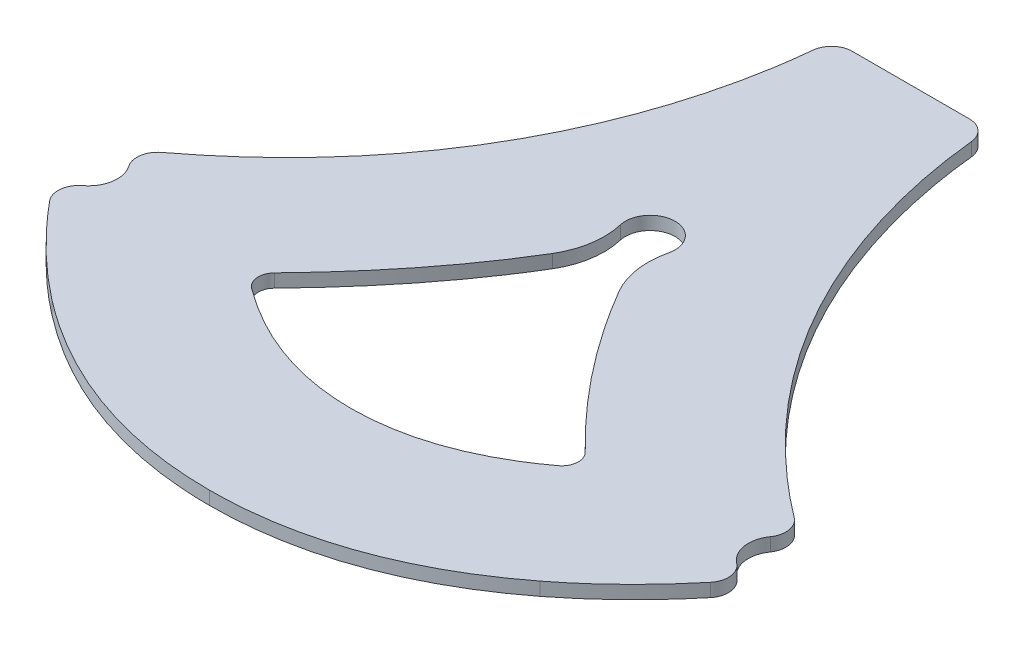
SolidWorks part; units mm, degrees
material "Default Heavy"
ref_plane "Front \"XY\"" through (0, 0, 0) normal (0, 0, 1) x (1, 0, 0)
ref_plane "Top \"XZ\"" through (0, 0, 0) normal (0, 1, 0) x (1, 0, 0)
ref_plane "Right \"YZ\"" through (0, 0, 0) normal (1, 0, 0) x (0, 0, -1)
sketch "Sketch1" plane through (0, -12.0818, 0) normal (0, 1, 0) x (1, 0, 0)
  line L4 (7.0683, 41.6006) -> (-7.0595, 41.6006)
  line L6 (7.0683, 41.6006) -> (-7.0595, 41.6006)
  arc A33 (-38.13, -10.5891) -> (-38.673, -14.0195) centre (-36.6252, -12.5855) ccw
  arc A34 (-39.4206, -18.8125) -> (-38.673, -14.0195) centre (-41.54, -16.0271) ccw
  arc A38 (-39.4206, -18.8125) -> (-39.832, -22.397) centre (-37.9068, -20.8021) ccw
  arc A39 (39.8378, -22.4011) -> (39.4269, -18.8166) centre (37.9129, -20.8059) ccw
  arc A40 (38.6795, -14.0241) -> (39.4269, -18.8166) centre (41.5466, -16.0315) ccw
  arc A41 (38.6795, -14.0241) -> (38.1364, -10.5939) centre (36.6316, -12.5902) ccw
  arc A42 (9.5562, 39.3464) -> (7.0683, 41.6006) centre (7.0683, 39.1006) ccw
  arc A43 (-7.0595, 41.6006) -> (-9.5474, 39.3464) centre (-7.0595, 39.1006) ccw
  arc A44 (-38.13, -10.5891) -> (-38.673, -14.0195) centre (-36.6252, -12.5855) ccw
  arc A45 (-39.4206, -18.8125) -> (-38.673, -14.0195) centre (-41.54, -16.0271) ccw
  arc A70 (-39.4206, -18.8125) -> (-39.832, -22.397) centre (-37.9068, -20.8021) ccw
  arc A71 (39.8378, -22.4011) -> (39.4269, -18.8166) centre (37.9129, -20.8059) ccw
  arc A72 (38.6795, -14.0241) -> (39.4269, -18.8166) centre (41.5466, -16.0315) ccw
  arc A73 (38.6795, -14.0241) -> (38.1364, -10.5939) centre (36.6316, -12.5902) ccw
  arc A74 (2.9171, 9.4772) -> (3.9511, 2.4687) centre (12.1546, 7.2595) ccw
  arc A75 (2.9171, 9.4772) -> (-2.9198, 9.4884) centre (0, 10.1775) ccw
  arc A81 (-4.0195, 2.4188) -> (-2.9198, 9.4884) centre (-12.1658, 7.3063) ccw
  arc A82 (-18.7595, -16.3733) -> (-18.4947, -19.3822) centre (-17.321, -17.7628) ccw
  arc A83 (18.4703, -19.4074) -> (18.7041, -16.3632) centre (17.2989, -17.7863) ccw
  arc A84 (2.9171, 9.4772) -> (3.9511, 2.4687) centre (12.1546, 7.2595) ccw
  arc A85 (2.9171, 9.4772) -> (-2.9198, 9.4884) centre (0, 10.1775) ccw
  arc A86 (-4.0195, 2.4188) -> (-2.9198, 9.4884) centre (-12.1658, 7.3063) ccw
  arc A87 (-18.7595, -16.3733) -> (-18.4947, -19.3822) centre (-17.321, -17.7628) ccw
  arc A88 (18.4703, -19.4074) -> (18.7041, -16.3632) centre (17.2989, -17.7863) ccw
  arc A89 (9.5562, 39.3464) -> (7.0683, 41.6006) centre (7.0683, 39.1006) ccw
  arc A90 (-7.0595, 41.6006) -> (-9.5474, 39.3464) centre (-7.0595, 39.1006) ccw
  spline S20 degree 3 poles (-361.1357, -9006.2412) (408.2007, 1023.6766) (-189.9273, 124.0647) (90.5106, -150.5904) (675.6401, 247.861) (5925.1762, 6688.6559) knots -44.189991 -44.189991 -44.189991 -44.189991 0.5 0.5 36.656885 36.656885 36.656885 36.656885 only from (-39.832, -22.397) to (-29.4307, -32.5394)
  spline S21 degree 3 poles (-5458.9807, -7160.509) (288.0292, 1163.494) (-198.9613, 61.9288) (-20.4604, -38.26) (-18.0451, -39.3754) (-14.2816, -40.7314) (-13.0141, -41.1265) (-10.4626, -41.8017) (-9.1771, -42.0821) (532.9278, -135.8371) (2755.8216, 9607.2036) (1449.1515, -1290.1086) knots -18.691493 -18.691493 -18.691493 -18.691493 0.25 0.25 0.5 0.5 0.625 0.625 0.75 0.75 52.944378 52.944378 52.944378 52.944378 only from (-29.4307, -32.5394) to (0.0044, -42.9764)
  spline S22 degree 3 poles (-83.0583, -8924.3195) (-816.3421, 2678.0036) (-279.5813, -92.3971) (9.2595, -42.0675) (10.5562, -41.7816) (13.107, -41.1014) (14.3628, -40.7068) (16.8364, -39.8119) (18.0542, -39.3118) (20.453, -38.2088) (21.6352, -37.6052) (199.0578, 61.9922) (-287.9926, 1164.7432) (5456.6153, -7163.0256) knots -27.11452 -27.11452 -27.11452 -27.11452 0.25 0.25 0.375 0.375 0.5 0.5 0.625 0.625 0.75 0.75 19.719987 19.719987 19.719987 19.719987 only from (0.0044, -42.9764) to (29.4355, -32.5422)
  spline S23 degree 3 poles (-2497.4272, 8560.7562) (-655.9836, 202.49) (-86.0813, -146.2484) (206.1007, 139.8782) (-568.1525, 1188.8875) (5991.7805, -6735.1983) knots -34.384152 -34.384152 -34.384152 -34.384152 0.5 0.5 49.852417 49.852417 49.852417 49.852417 only from (29.4355, -32.5422) to (39.8378, -22.4011)
  spline S24 degree 3 poles (-5230.3909, -7151.1905) (1948.6338, 1128.9285) (244.6684, -243.4554) (26.3668, 0.3497) (25.5637, 1.2946) (24.0142, 3.2162) (23.2668, 4.194) (21.1067, 7.1786) (19.7757, 9.2361) (17.3325, 13.4873) (16.2204, 15.6811) (14.7199, 19.076) (14.2467, 20.228) (13.3659, 22.5445) (12.9574, 23.7106) (11.8252, 27.2324) (11.1946, 29.6112) (-27.552, 214.2746) (637.6915, 571.7004) (8574.638, 2739.8271) knots -16.155295 -16.155295 -16.155295 -16.155295 0.25 0.25 0.3125 0.3125 0.375 0.375 0.5 0.5 0.625 0.625 0.6875 0.6875 0.75 0.75 0.875 0.875 10.328449 10.328449 10.328449 10.328449 only from (38.1364, -10.5939) to (9.5562, 39.3464)
  spline S25 degree 3 poles (-8658.0975, 2453.4979) (-703.6804, 575.1627) (29.2386, 221.9755) (-11.1913, 29.5904) (-11.826, 27.1987) (-13.3506, 22.4691) (-14.2312, 20.1617) (-16.2194, 15.6707) (-17.3273, 13.4849) (-19.7716, 9.2335) (-21.1079, 7.1677) (-23.287, 4.1607) (-24.0441, 3.1719) (-25.6008, 1.2452) (-26.402, 0.3048) (-261.0781, -261.3629) (-2273.2675, 1279.1753) (5393.2872, -6983.9462) knots -9.693628 -9.693628 -9.693628 -9.693628 0.125 0.125 0.25 0.25 0.375 0.375 0.5 0.5 0.625 0.625 0.6875 0.6875 0.75 0.75 18.503939 18.503939 18.503939 18.503939 only from (-9.5474, 39.3464) to (-38.13, -10.5891)
  spline S26 degree 3 poles (-39.832, -22.397) (-38.2832, -24.2664) (-36.6431, -26.0587) (-33.1743, -29.4559) (-31.352, -31.0548) (-29.4307, -32.5394) knots 0 0 0 0 0.5 0.5 1 1 1 1
  spline S27 degree 3 poles (-29.4307, -32.5394) (-27.3206, -34.1699) (-25.1109, -35.6497) (-20.4604, -38.26) (-18.0451, -39.3754) (-14.2816, -40.7314) (-13.0141, -41.1265) (-10.4626, -41.8017) (-9.1771, -42.0821) (-5.2915, -42.7541) (-2.6626, -42.9764) (0.0044, -42.9764) knots 0 0 0 0 0.25 0.25 0.5 0.5 0.625 0.625 0.75 0.75 1 1 1 1
  spline S28 degree 3 poles (0.0044, -42.9764) (2.6717, -42.9764) (5.3193, -42.7541) (9.2595, -42.0675) (10.5562, -41.7816) (13.107, -41.1014) (14.3628, -40.7068) (16.8364, -39.8119) (18.0542, -39.3118) (20.453, -38.2088) (21.6352, -37.6052) (25.1195, -35.6492) (27.3272, -34.1709) (29.4355, -32.5422) knots 0 0 0 0 0.25 0.25 0.375 0.375 0.5 0.5 0.625 0.625 0.75 0.75 1 1 1 1
  spline S29 degree 3 poles (29.4355, -32.5422) (31.3567, -31.058) (33.1832, -29.4556) (36.6518, -26.0589) (38.289, -24.2701) (39.8378, -22.4011) knots 0 0 0 0 0.5 0.5 1 1 1 1
  spline S30 degree 3 poles (38.1364, -10.5939) (34.1686, -7.603) (30.5094, -4.2768) (26.3668, 0.3497) (25.5637, 1.2946) (24.0142, 3.2162) (23.2668, 4.194) (21.1067, 7.1786) (19.7757, 9.2361) (17.3325, 13.4873) (16.2204, 15.6811) (14.7199, 19.076) (14.2467, 20.228) (13.3659, 22.5445) (12.9574, 23.7106) (11.8252, 27.2324) (11.1946, 29.6112) (10.1833, 34.4309) (9.8006, 36.8714) (9.5562, 39.3464) knots 0 0 0 0 0.25 0.25 0.3125 0.3125 0.375 0.375 0.5 0.5 0.625 0.625 0.6875 0.6875 0.75 0.75 0.875 0.875 1 1 1 1
  spline S31 degree 3 poles (-9.5474, 39.3464) (-9.7918, 36.8722) (-10.1748, 34.4273) (-11.1913, 29.5904) (-11.826, 27.1987) (-13.3506, 22.4691) (-14.2312, 20.1617) (-16.2194, 15.6707) (-17.3273, 13.4849) (-19.7716, 9.2335) (-21.1079, 7.1677) (-23.287, 4.1607) (-24.0441, 3.1719) (-25.6008, 1.2452) (-26.402, 0.3048) (-30.5182, -4.2848) (-34.1638, -7.5994) (-38.13, -10.5891) knots 0 0 0 0 0.125 0.125 0.25 0.25 0.375 0.375 0.5 0.5 0.625 0.625 0.6875 0.6875 0.75 0.75 1 1 1 1
  spline S33 degree 3 poles (-8423.8862, 3070.8277) (-196.453, 631.0114) (110.0496, 145.3413) (-12.0871, -8.969) (-13.3692, -10.4966) (-15.3493, -12.7369) (-16.0189, -13.4752) (-80.2953, -82.6348) (-244.7018, -61.9377) (6531.7724, -6177.7669) knots -23.901351 -23.901351 -23.901351 -23.901351 0.5 0.5 0.75 0.75 0.875 0.875 12.588314 12.588314 12.588314 12.588314 only from (-4.0195, 2.4188) to (-18.7595, -16.3733)
  spline S34 degree 3 poles (-4293.5555, -7936.5231) (-50.3766, 110.0419) (-54.4223, 5.6325) (-17.1355, -20.3479) (-16.7908, -20.5799) (-15.747, -21.2574) (-15.0382, -21.6843) (-12.8707, -22.886) (-11.3707, -23.5815) (-9.0251, -24.4414) (-8.2235, -24.6981) (-6.6138, -25.1376) (-5.804, -25.3212) (-3.3598, -25.7638) (-1.7106, -25.9143) (0.7936, -25.9184) (1.6348, -25.8822) (3.2938, -25.7361) (4.1158, -25.6264) (6.5599, -25.19) (8.16, -24.7562) (10.518, -23.8999) (11.2939, -23.5809) (12.8082, -22.888) (13.5495, -22.5131) (15.0027, -21.7105) (15.7146, -21.2829) (16.7621, -20.605) (17.1079, -20.3728) (54.5018, 5.6202) (48.809, 108.0735) (4514.6713, -7812.9902) knots -3.348669 -3.348669 -3.348669 -3.348669 0.03125 0.03125 0.0625 0.0625 0.125 0.125 0.25 0.25 0.3125 0.3125 0.375 0.375 0.5 0.5 0.5625 0.5625 0.625 0.625 0.75 0.75 0.8125 0.8125 0.875 0.875 0.9375 0.9375 0.96875 0.96875 4.349856 4.349856 4.349856 4.349856 only from (-18.4947, -19.3822) to (18.4703, -19.4074)
  spline S53 degree 3 poles (-6295.3391, -6420.8441) (241.7112, -32.3679) (75.1144, -75.141) (15.8981, -13.5111) (15.217, -12.7784) (13.2098, -10.546) (11.9226, -9.0147) (-199.8505, 260.9693) (1210.8718, 1641.0125) (7479.9657, 4881.6019) knots -10.431592 -10.431592 -10.431592 -10.431592 0.125 0.125 0.25 0.25 0.5 0.5 43.112125 43.112125 43.112125 43.112125 only from (18.7041, -16.3632) to (3.9511, 2.4687)
  spline S54 degree 3 poles (-4.0195, 2.4188) (-6.0734, -1.0046) (-8.3712, -4.2742) (-12.0871, -8.969) (-13.3692, -10.4966) (-15.3493, -12.7369) (-16.0189, -13.4752) (-17.3762, -14.9357) (-18.0664, -15.6558) (-18.7595, -16.3733) knots 0 0 0 0 0.5 0.5 0.75 0.75 0.875 0.875 1 1 1 1
  spline S55 degree 3 poles (-18.4947, -19.3822) (-18.1567, -19.6272) (-17.8187, -19.8719) (-17.1355, -20.3479) (-16.7908, -20.5799) (-15.747, -21.2574) (-15.0382, -21.6843) (-12.8707, -22.886) (-11.3707, -23.5815) (-9.0251, -24.4414) (-8.2235, -24.6981) (-6.6138, -25.1376) (-5.804, -25.3212) (-3.3598, -25.7638) (-1.7106, -25.9143) (0.7936, -25.9184) (1.6348, -25.8822) (3.2938, -25.7361) (4.1158, -25.6264) (6.5599, -25.19) (8.16, -24.7562) (10.518, -23.8999) (11.2939, -23.5809) (12.8082, -22.888) (13.5495, -22.5131) (15.0027, -21.7105) (15.7146, -21.2829) (16.7621, -20.605) (17.1079, -20.3728) (17.7928, -19.8967) (18.1316, -19.6522) (18.4703, -19.4074) knots 0 0 0 0 0.03125 0.03125 0.0625 0.0625 0.125 0.125 0.25 0.25 0.3125 0.3125 0.375 0.375 0.5 0.5 0.5625 0.5625 0.625 0.625 0.75 0.75 0.8125 0.8125 0.875 0.875 0.9375 0.9375 0.96875 0.96875 1 1 1 1
  spline S56 degree 3 poles (18.7041, -16.3632) (17.9921, -15.6602) (17.284, -14.9535) (15.8981, -13.5111) (15.217, -12.7784) (13.2098, -10.546) (11.9226, -9.0147) (8.217, -4.2905) (5.9698, -0.988) (3.9511, 2.4687) knots 0 0 0 0 0.125 0.125 0.25 0.25 0.5 0.5 1 1 1 1
  dimension "D1" = 0.5
  dimension "D2" = 0.5
extrude "Boss-Extrude1" add sketch "Sketch1" along normal blind 1.6
sketch "Sketch2" plane through (0, -10.4818, 0) normal (0, 1, 0) x (1, 0, 0)
  line L0 (0.0044, 41.6006) -> (0.0044, 33.6006)
  line L1 (7.0683, 41.6006) -> (-7.0595, 41.6006) construction
  line L2 (0.0044, -42.9764) -> (0.0044, -34.9764)
  line L3 (-25.2799, -35.4613) -> (-20.9815, -28.7141)
  line L4 (25.2885, -35.4609) -> (20.9901, -28.7138)
  line L5 (7.0683, 41.6006) -> (-7.0595, 41.6006)
  arc A0 (9.5562, 39.3464) -> (7.0683, 41.6006) centre (7.0683, 39.1006) ccw construction
  arc A1 (-7.0595, 41.6006) -> (-9.5474, 39.3464) centre (-7.0595, 39.1006) ccw construction
  arc A2 (-38.13, -10.5891) -> (-38.673, -14.0195) centre (-36.6252, -12.5855) ccw construction
  arc A3 (-39.4206, -18.8125) -> (-38.673, -14.0195) centre (-41.54, -16.0271) ccw construction
  arc A4 (-39.4206, -18.8125) -> (-39.832, -22.397) centre (-37.9068, -20.8021) ccw construction
  arc A5 (39.8378, -22.4011) -> (39.4269, -18.8166) centre (37.9129, -20.8059) ccw construction
  arc A6 (38.6795, -14.0241) -> (39.4269, -18.8166) centre (41.5466, -16.0315) ccw construction
  arc A7 (38.6795, -14.0241) -> (38.1364, -10.5939) centre (36.6316, -12.5902) ccw construction
  arc A8 (9.5562, 39.3464) -> (7.0683, 41.6006) centre (7.0683, 39.1006) ccw
  arc A9 (-7.0595, 41.6006) -> (-9.5474, 39.3464) centre (-7.0595, 39.1006) ccw
  arc A10 (-38.13, -10.5891) -> (-38.673, -14.0195) centre (-36.6252, -12.5855) ccw
  arc A11 (-39.4206, -18.8125) -> (-38.673, -14.0195) centre (-41.54, -16.0271) ccw
  arc A12 (-39.4206, -18.8125) -> (-39.832, -22.397) centre (-37.9068, -20.8021) ccw
  arc A13 (39.8378, -22.4011) -> (39.4269, -18.8166) centre (37.9129, -20.8059) ccw
  arc A14 (38.6795, -14.0241) -> (39.4269, -18.8166) centre (41.5466, -16.0315) ccw
  arc A15 (38.6795, -14.0241) -> (38.1364, -10.5939) centre (36.6316, -12.5902) ccw
  arc A16 (-18.7595, -16.3733) -> (-18.4947, -19.3822) centre (-17.321, -17.7628) ccw construction
  arc A17 (18.4703, -19.4074) -> (18.7041, -16.3632) centre (17.2989, -17.7863) ccw construction
  arc A18 (2.9171, 9.4772) -> (3.9511, 2.4687) centre (12.1546, 7.2595) ccw construction
  arc A19 (2.9171, 9.4772) -> (-2.9198, 9.4884) centre (0, 10.1775) ccw construction
  arc A20 (-4.0195, 2.4188) -> (-2.9198, 9.4884) centre (-12.1658, 7.3063) ccw construction
  arc A21 (-18.7595, -16.3733) -> (-18.4947, -19.3822) centre (-17.321, -17.7628) ccw
  arc A22 (18.4703, -19.4074) -> (18.7041, -16.3632) centre (17.2989, -17.7863) ccw
  arc A23 (2.9171, 9.4772) -> (3.9511, 2.4687) centre (12.1546, 7.2595) ccw
  arc A24 (2.9171, 9.4772) -> (-2.9198, 9.4884) centre (0, 10.1775) ccw
  arc A25 (-4.0195, 2.4188) -> (-2.9198, 9.4884) centre (-12.1658, 7.3063) ccw
  spline S0 degree 3 poles (-1424.0562, -1442.6952) (28.6907, 516.1598) (-137.4092, 27.3809) (-20.4604, -38.26) (-18.0451, -39.3754) (-14.2816, -40.7314) (-13.0141, -41.1265) (-10.4626, -41.8017) (-9.1771, -42.0821) (158.4711, -71.0762) (483.979, 830.8672) (816.9599, 1776.512) knots -12.073737 -12.073737 -12.073737 -12.073737 0.25 0.25 0.5 0.5 0.625 0.625 0.75 0.75 16.804983 16.804983 16.804983 16.804983 only from (-29.4307, -32.5394) to (0.0044, -42.9764) construction
  spline S1 degree 3 poles (-29.4307, -32.5394) (-27.3206, -34.1699) (-25.1109, -35.6497) (-20.4604, -38.26) (-18.0451, -39.3754) (-14.2816, -40.7314) (-13.0141, -41.1265) (-10.4626, -41.8017) (-9.1771, -42.0821) (-5.2915, -42.7541) (-2.6626, -42.9764) (0.0044, -42.9764) knots 0 0 0 0 0.25 0.25 0.5 0.5 0.625 0.625 0.75 0.75 1 1 1 1 construction
  spline S2 degree 3 poles (0.0044, -42.9764) (2.6717, -42.9764) (5.3193, -42.7541) (9.2595, -42.0675) (10.5562, -41.7816) (13.107, -41.1014) (14.3628, -40.7068) (16.8364, -39.8119) (18.0542, -39.3118) (20.453, -38.2088) (21.6352, -37.6052) (25.1195, -35.6492) (27.3272, -34.1709) (29.4355, -32.5422) knots 0 0 0 0 0.25 0.25 0.375 0.375 0.5 0.5 0.625 0.625 0.75 0.75 1 1 1 1 construction
  spline S3 degree 3 poles (-440.2453, -1934.8699) (-519.17, 1279.8396) (-194.086, -77.4998) (9.2595, -42.0675) (10.5562, -41.7816) (13.107, -41.1014) (14.3628, -40.7068) (16.8364, -39.8119) (18.0542, -39.3118) (20.453, -38.2088) (21.6352, -37.6052) (137.4809, 27.4256) (-28.6443, 516.76) (1423.6331, -1443.0733) knots -18.977772 -18.977772 -18.977772 -18.977772 0.25 0.25 0.375 0.375 0.5 0.5 0.625 0.625 0.75 0.75 13.09281 13.09281 13.09281 13.09281 only from (0.0044, -42.9764) to (29.4355, -32.5422) construction
  spline S4 degree 3 poles (-1867.0337, 761.7677) (-214.1809, 300.124) (11.968, 139.7937) (-11.1913, 29.5904) (-11.826, 27.1987) (-13.3506, 22.4691) (-14.2312, 20.1617) (-16.2194, 15.6707) (-17.3273, 13.4849) (-19.7716, 9.2335) (-21.1079, 7.1677) (-23.287, 4.1607) (-24.0441, 3.1719) (-25.6008, 1.2452) (-26.402, 0.3048) (-188.6003, -180.5489) (-1196.8152, 497.2845) (713.0433, -1780.6166) knots -5.445972 -5.445972 -5.445972 -5.445972 0.125 0.125 0.25 0.25 0.375 0.375 0.5 0.5 0.625 0.625 0.6875 0.6875 0.75 0.75 13.001475 13.001475 13.001475 13.001475 only from (-9.5474, 39.3464) to (-38.13, -10.5891) construction
  spline S5 degree 3 poles (34.5014, -2019.1221) (83.4289, 488.7085) (-136.0537, 71.302) (37.1209, -98.3016) (260.7778, 3.0906) (1432.5412, 1322.2518) knots -28.658886 -28.658886 -28.658886 -28.658886 0.5 0.5 21.265271 21.265271 21.265271 21.265271 only from (-39.832, -22.397) to (-29.4307, -32.5394) construction
  spline S6 degree 3 poles (-807.9187, 1769.9142) (-261.6301, -5.9472) (-36.08, -97.2833) (147.6142, 82.6039) (-149.4521, 574.9626) (1506.1611, -1362.4779) knots -19.968685 -19.968685 -19.968685 -19.968685 0.5 0.5 32.99067 32.99067 32.99067 32.99067 only from (29.4355, -32.5422) to (39.8378, -22.4011) construction
  spline S7 degree 3 poles (-725.1623, -1795.2036) (1009.533, 415.4628) (175.0079, -165.6568) (26.3668, 0.3497) (25.5637, 1.2946) (24.0142, 3.2162) (23.2668, 4.194) (21.1067, 7.1786) (19.7757, 9.2361) (17.3325, 13.4873) (16.2204, 15.6811) (14.7199, 19.076) (14.2467, 20.228) (13.3659, 22.5445) (12.9574, 23.7106) (11.8252, 27.2324) (11.1946, 29.6112) (-11.0987, 135.8594) (195.4726, 296.5607) (1845.1699, 816.6095) knots -10.900393 -10.900393 -10.900393 -10.900393 0.25 0.25 0.3125 0.3125 0.375 0.375 0.5 0.5 0.625 0.625 0.6875 0.6875 0.75 0.75 0.875 0.875 6.261071 6.261071 6.261071 6.261071 only from (38.1364, -10.5939) to (9.5562, 39.3464) construction
  spline S8 degree 3 poles (-9.5474, 39.3464) (-9.7918, 36.8722) (-10.1748, 34.4273) (-11.1913, 29.5904) (-11.826, 27.1987) (-13.3506, 22.4691) (-14.2312, 20.1617) (-16.2194, 15.6707) (-17.3273, 13.4849) (-19.7716, 9.2335) (-21.1079, 7.1677) (-23.287, 4.1607) (-24.0441, 3.1719) (-25.6008, 1.2452) (-26.402, 0.3048) (-30.5182, -4.2848) (-34.1638, -7.5994) (-38.13, -10.5891) knots 0 0 0 0 0.125 0.125 0.25 0.25 0.375 0.375 0.5 0.5 0.625 0.625 0.6875 0.6875 0.75 0.75 1 1 1 1
  spline S9 degree 3 poles (-39.832, -22.397) (-38.2832, -24.2664) (-36.6431, -26.0587) (-33.1743, -29.4559) (-31.352, -31.0548) (-29.4307, -32.5394) knots 0 0 0 0 0.5 0.5 1 1 1 1
  spline S10 degree 3 poles (-29.4307, -32.5394) (-27.3206, -34.1699) (-25.1109, -35.6497) (-20.4604, -38.26) (-18.0451, -39.3754) (-14.2816, -40.7314) (-13.0141, -41.1265) (-10.4626, -41.8017) (-9.1771, -42.0821) (-5.2915, -42.7541) (-2.6626, -42.9764) (0.0044, -42.9764) knots 0 0 0 0 0.25 0.25 0.5 0.5 0.625 0.625 0.75 0.75 1 1 1 1
  spline S11 degree 3 poles (0.0044, -42.9764) (2.6717, -42.9764) (5.3193, -42.7541) (9.2595, -42.0675) (10.5562, -41.7816) (13.107, -41.1014) (14.3628, -40.7068) (16.8364, -39.8119) (18.0542, -39.3118) (20.453, -38.2088) (21.6352, -37.6052) (25.1195, -35.6492) (27.3272, -34.1709) (29.4355, -32.5422) knots 0 0 0 0 0.25 0.25 0.375 0.375 0.5 0.5 0.625 0.625 0.75 0.75 1 1 1 1
  spline S12 degree 3 poles (29.4355, -32.5422) (31.3567, -31.058) (33.1832, -29.4556) (36.6518, -26.0589) (38.289, -24.2701) (39.8378, -22.4011) knots 0 0 0 0 0.5 0.5 1 1 1 1
  spline S13 degree 3 poles (38.1364, -10.5939) (34.1686, -7.603) (30.5094, -4.2768) (26.3668, 0.3497) (25.5637, 1.2946) (24.0142, 3.2162) (23.2668, 4.194) (21.1067, 7.1786) (19.7757, 9.2361) (17.3325, 13.4873) (16.2204, 15.6811) (14.7199, 19.076) (14.2467, 20.228) (13.3659, 22.5445) (12.9574, 23.7106) (11.8252, 27.2324) (11.1946, 29.6112) (10.1833, 34.4309) (9.8006, 36.8714) (9.5562, 39.3464) knots 0 0 0 0 0.25 0.25 0.3125 0.3125 0.375 0.375 0.5 0.5 0.625 0.625 0.6875 0.6875 0.75 0.75 0.875 0.875 1 1 1 1
  spline S14 degree 3 poles (-1759.4085, 935.1256) (-16.3001, 286.9476) (60.173, 82.3261) (-12.0871, -8.969) (-13.3692, -10.4966) (-15.3493, -12.7369) (-16.0189, -13.4752) (-55.5636, -56.0242) (-132.0789, -64.5568) (1360.9324, -1460.7289) knots -13.834561 -13.834561 -13.834561 -13.834561 0.5 0.5 0.75 0.75 0.875 0.875 8.033279 8.033279 8.033279 8.033279 only from (-4.0195, 2.4188) to (-18.7595, -16.3733) construction
  spline S15 degree 3 poles (-1013.0538, -1753.8668) (-47.2995, 40.5796) (-40.0167, -4.405) (-17.1355, -20.3479) (-16.7908, -20.5799) (-15.747, -21.2574) (-15.0382, -21.6843) (-12.8707, -22.886) (-11.3707, -23.5815) (-9.0251, -24.4414) (-8.2235, -24.6981) (-6.6138, -25.1376) (-5.804, -25.3212) (-3.3598, -25.7638) (-1.7106, -25.9143) (0.7936, -25.9184) (1.6348, -25.8822) (3.2938, -25.7361) (4.1158, -25.6264) (6.5599, -25.19) (8.16, -24.7562) (10.518, -23.8999) (11.2939, -23.5809) (12.8082, -22.888) (13.5495, -22.5131) (15.0027, -21.7105) (15.7146, -21.2829) (16.7621, -20.605) (17.1079, -20.3728) (40.0478, -4.427) (46.7456, 39.8102) (1061.6633, -1725.0478) knots -2.030772 -2.030772 -2.030772 -2.030772 0.03125 0.03125 0.0625 0.0625 0.125 0.125 0.25 0.25 0.3125 0.3125 0.375 0.375 0.5 0.5 0.5625 0.5625 0.625 0.625 0.75 0.75 0.8125 0.8125 0.875 0.875 0.9375 0.9375 0.96875 0.96875 3.030862 3.030862 3.030862 3.030862 only from (-18.4947, -19.3822) to (18.4703, -19.4074) construction
  spline S16 degree 3 poles (-1313.5745, -1505.1428) (128.6195, -49.9528) (52.388, -51.4883) (15.8981, -13.5111) (15.217, -12.7784) (13.2098, -10.546) (11.9226, -9.0147) (-97.6997, 130.74) (223.5957, 563.5363) (1416.2462, 1393.1308) knots -6.332144 -6.332144 -6.332144 -6.332144 0.125 0.125 0.25 0.25 0.5 0.5 22.437176 22.437176 22.437176 22.437176 only from (18.7041, -16.3632) to (3.9511, 2.4687) construction
  spline S17 degree 3 poles (-4.0195, 2.4188) (-6.0734, -1.0046) (-8.3712, -4.2742) (-12.0871, -8.969) (-13.3692, -10.4966) (-15.3493, -12.7369) (-16.0189, -13.4752) (-17.3762, -14.9357) (-18.0664, -15.6558) (-18.7595, -16.3733) knots 0 0 0 0 0.5 0.5 0.75 0.75 0.875 0.875 1 1 1 1
  spline S18 degree 3 poles (-18.4947, -19.3822) (-18.1567, -19.6272) (-17.8187, -19.8719) (-17.1355, -20.3479) (-16.7908, -20.5799) (-15.747, -21.2574) (-15.0382, -21.6843) (-12.8707, -22.886) (-11.3707, -23.5815) (-9.0251, -24.4414) (-8.2235, -24.6981) (-6.6138, -25.1376) (-5.804, -25.3212) (-3.3598, -25.7638) (-1.7106, -25.9143) (0.7936, -25.9184) (1.6348, -25.8822) (3.2938, -25.7361) (4.1158, -25.6264) (6.5599, -25.19) (8.16, -24.7562) (10.518, -23.8999) (11.2939, -23.5809) (12.8082, -22.888) (13.5495, -22.5131) (15.0027, -21.7105) (15.7146, -21.2829) (16.7621, -20.605) (17.1079, -20.3728) (17.7928, -19.8967) (18.1316, -19.6522) (18.4703, -19.4074) knots 0 0 0 0 0.03125 0.03125 0.0625 0.0625 0.125 0.125 0.25 0.25 0.3125 0.3125 0.375 0.375 0.5 0.5 0.5625 0.5625 0.625 0.625 0.75 0.75 0.8125 0.8125 0.875 0.875 0.9375 0.9375 0.96875 0.96875 1 1 1 1
  spline S19 degree 3 poles (18.7041, -16.3632) (17.9921, -15.6602) (17.284, -14.9535) (15.8981, -13.5111) (15.217, -12.7784) (13.2098, -10.546) (11.9226, -9.0147) (8.217, -4.2905) (5.9698, -0.988) (3.9511, 2.4687) knots 0 0 0 0 0.125 0.125 0.25 0.25 0.5 0.5 1 1 1 1
  dimension "D1" = 8
  dimension "D2" = 32.5
  dimension "D3" = 32.5
equation "\"D3@Sketch2\"=\"D2@Sketch2\""
